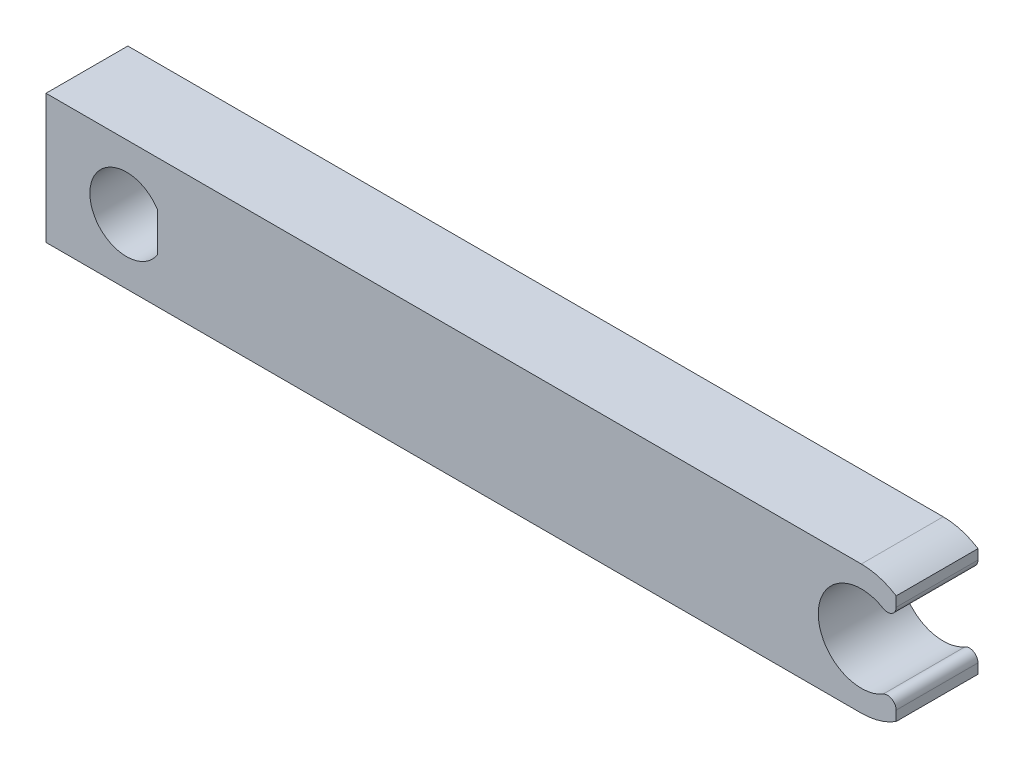
SolidWorks part; units mm, degrees
ref_plane "前视基准面" through (0, 0, 0) normal (0, 0, 1) x (1, 0, 0)
ref_plane "上视基准面" through (0, 0, 0) normal (0, 1, 0) x (1, 0, 0)
ref_plane "右视基准面" through (0, 0, 0) normal (1, 0, 0) x (0, 0, -1)
sketch "草图1" plane through (0, 0, 0) normal (0, 0, 1) x (1, 0, 0)
  line L0 (-11.3265, 4.4008) -> (-11.4061, 4.2597)
  line L1 (-14.327, 0) -> (53.9157, 0)
  line L2 (-14.327, 0) -> (-14.327, 12)
  line L3 (-14.327, 12) -> (53.9157, 12)
  line L4 (53.9157, 0) -> (53.9157, 12)
  line L5 (-11.4061, 4.2597) -> (-11.4061, 7.7403)
  line L6 (-14.327, 12) -> (-21.8019, 12)
  line L7 (-21.8019, 12) -> (-21.8019, 0)
  line L8 (-21.8019, 0) -> (-14.327, 0)
  line L9 (53.9157, 6) -> (57.1503, 11.0535)
  line L10 (57.1503, 11.0535) -> (57.1503, 0.9465)
  line L11 (-11.4061, 6) -> (-10.927, 6)
  circle A0 centre (-14.327, 6) radius 3.4
  circle A1 centre (53.9157, 6) radius 6
  circle A2 centre (53.9157, 6) radius 4
extrude "凸台-拉伸2" add sketch "草图1" along normal blind 7.6 contours A1 L3 L2 A0 L1 | A0 L2 L6 L7 L8 | A2 L4 A1 | A2 L4 A1 L10 | A2 L9 A1 L4 | A2 L10 L9 | L0 L5
sketch "草图2" plane through (0, 0, 7.6) normal (0, 0, 1) x (1, 0, 0)
  line L1 (-11.427, 4.2252) -> (-4.8979, 4.2252)
  line L2 (-11.427, 4.2252) -> (-11.427, 10.2338)
  line L3 (-11.427, 10.2338) -> (-4.8979, 10.2338)
  line L4 (-4.8979, 4.2252) -> (-4.8979, 10.2338)
  circle A0 centre (-14.327, 6) radius 3.4 construction
extrude "凸台-拉伸5" add sketch "草图2" against normal blind 7.5
fillet "圆角1" radius 0.8 2 edges at (57.1503, 8.3532, 3.8) (57.1503, 3.6468, 3.8)
